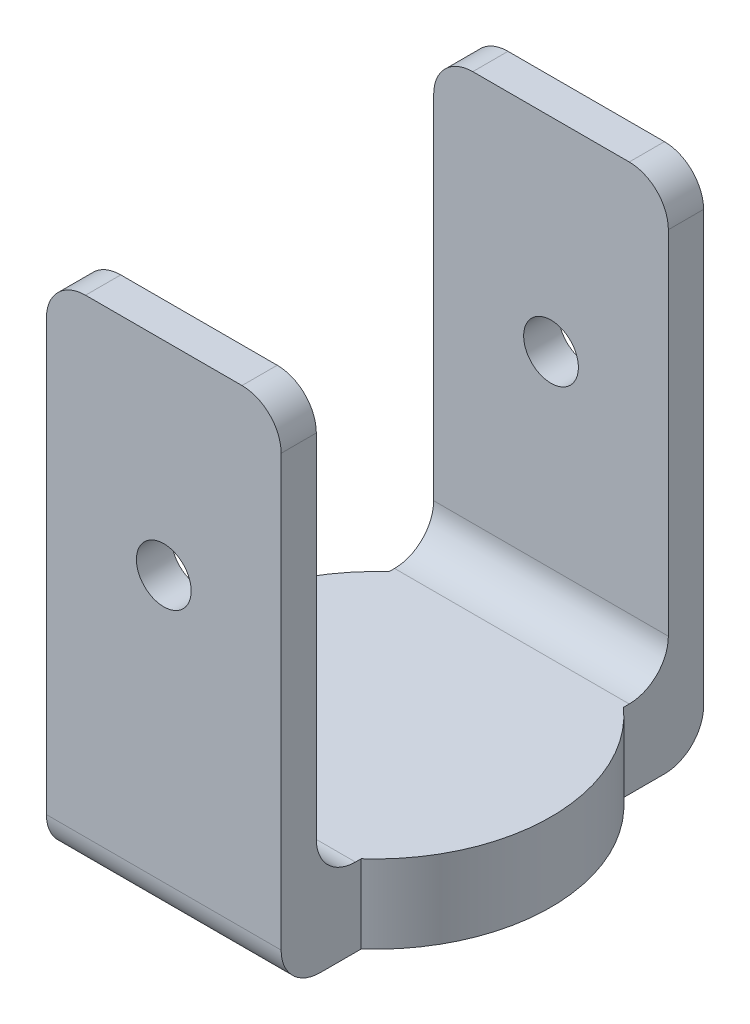
SolidWorks part; units mm, degrees
material "Nylon 6/10"
ref_plane "Front Plane" through (0, 0, 0) normal (0, 0, 1) x (1, 0, 0)
ref_plane "Top Plane" through (0, 0, 0) normal (0, 1, 0) x (1, 0, 0)
ref_plane "Right Plane" through (0, 0, 0) normal (1, 0, 0) x (0, 0, -1)
sketch "Sketch1" plane through (0, 0, 0) normal (1, 0, 0) x (0, 0, -1)
  line L0 (0, 0) -> (0, -65)
  line L1 (0, -65) -> (54, -65)
  line L2 (54, -65) -> (54, 0)
  line L3 (54, 0) -> (49.5, 0)
  line L4 (49.5, 0) -> (49.5, -55)
  line L5 (49.5, -55) -> (4.5, -55)
  line L6 (4.5, -55) -> (4.5, 0)
  line L7 (4.5, 0) -> (0, 0)
  dimension "D1" = 4.5
  dimension "D2" = 4.5
  dimension "D3" = 65
  dimension "D4" = 10
  dimension "D5" = 54
extrude "Boss-Extrude1" add sketch "Sketch1" along normal blind 30
sketch "Sketch3" plane through (0, -65, 0) normal (0, -1, 0) x (1, 0, 0)
  line L0 (30, 0) -> (30, -54) construction
  line L4 (30, 0) -> (0, 0) construction
  circle A0 centre (15, -27) radius 22.5
  point P10 (15, 0)
  point P13 (30, -27)
  dimension "D1" = 45
extrude "Boss-Extrude2" add sketch "Sketch3" against normal blind 10
fillet "Fillet2" radius 5 8 edges at (15, -65, -54) (15, -65, 0) (15, -55, -4.5) (0, 0, -2.25) (30, 0, -2.25) (0, 0, -51.75) (30, 0, -51.75) (15, -55, -49.5)
sketch "Sketch4" plane through (0, 0, -54) normal (0, 0, -1) x (-1, 0, 0)
  line L1 (-25, 0) -> (-5, 0) construction
  circle A0 centre (-15, -26) radius 3.5
  point P6 (-15, 0)
  dimension "D1" = 7
extrude "Cut-Extrude1" cut sketch "Sketch4" against normal blind 70
